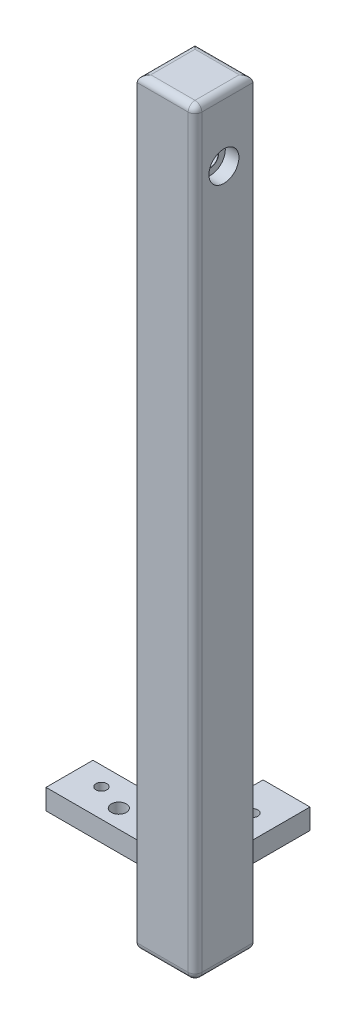
SolidWorks part; units mm, degrees
material "6061-T6 (SS)"
ref_plane "Front Plane" through (0, 0, 0) normal (0, 0, 1) x (1, 0, 0)
ref_plane "Top Plane" through (0, 0, 0) normal (0, 1, 0) x (1, 0, 0)
ref_plane "Right Plane" through (0, 0, 0) normal (1, 0, 0) x (0, 0, -1)
sketch "Sketch1" plane through (0, 0, 0) normal (0, 0, 1) x (1, 0, 0)
  line L0 (0, 0) -> (0, -111.5)
  line L1 (0, -111.5) -> (8.5, -111.5)
  line L2 (8.5, 0) -> (8.5, -111.5)
  line L7 (8.5, 0) -> (0, 0)
  dimension "D1" = 8.5
  dimension "D6" = 111.5
extrude "Boss-Extrude5" add sketch "Sketch1" along normal blind 8.5 contours L7 L0 L1 L2
hole_wizard "M5x0.8 Tapped Hole2" positions "Sketch26" profile "Sketch25" tap size "M5x0.8" standard "ANSI Metric"
sketch "Sketch26" plane through (0, -111.5, 0) normal (0, -1, 0) x (-1, 0, 0)
  point P0 (-4.25, -4.25)
sketch "Sketch25" plane through (4.25, -111.5, 4.25) normal (1, 0, 0) x (0, 0, -1)
  line L0 (0, 0) -> (0, 21.2618)
  line L1 (0, 21.2618) -> (2.1, 20)
  line L2 (2.1, 20) -> (2.1, 0)
  line L5 (2.1, 0) -> (0, 0)
  line L10 (0, 21.2618) -> (-2.1, 20) construction
  line L11 (0, -6.35) -> (0, 107.95) construction
  dimension "Tap Drill Dia." = 4.2
  dimension "Tap Drill Depth" = 20
  dimension "Drill Angle" = 118
cosmetic thread "Hole Thread4" parameters "D1"=10, "D2"=5
sketch "Sketch35" plane through (0, 0, 0) normal (-1, 0, 0) x (0, 0, 1)
  line L0 (0, 0) -> (0, -111.5) construction
  line L1 (0, -99) -> (8.5, -99)
  line L2 (0, -99) -> (0, -102)
  line L3 (0, -102) -> (8.5, -102)
  line L4 (8.5, -99) -> (8.5, -102)
  line L5 (8.5, 0) -> (8.5, -111.5) construction
  line L6 (8.5, -111.5) -> (0, -111.5) construction
  dimension "D1" = 9.5
  dimension "D2" = 3
extrude "Boss-Extrude6" add sketch "Sketch35" along normal blind 15
hole_wizard "Ø2.2 (2.2) Diameter Hole1" positions "Sketch37" profile "Sketch36" hole size "Ø2.2" standard "ANSI Metric"
sketch "Sketch37" plane through (0, -99, 0) normal (0, 1, 0) x (1, 0, 0)
  line L0 (-15, -8.5) -> (0, -8.5) construction
  line L2 (8.5, -8.5) -> (8.5, 0) construction
  point P0 (-7, -4.2)
  dimension "D1" = 4.3
  dimension "D2" = 15.5
sketch "Sketch36" plane through (-7, -99, 4.2) normal (1, 0, 0) x (0, 0, 1)
  line L0 (0, 0) -> (0, 13)
  line L1 (0, 13) -> (1.1, 13)
  line L2 (1.1, 13) -> (1.1, 0)
  line L5 (1.1, 0) -> (0, 0)
  line L10 (0, 13) -> (-1.1, 13) construction
  line L11 (0, -6.35) -> (0, 107.95) construction
  dimension "Hole Dia." = 2.2
  dimension "Hole Depth" = 13
  dimension "Drill Angle" = 180
hole_wizard "M2x0.4 Tapped Hole5" positions "Sketch39" profile "Sketch38" tap size "M2x0.4" standard "JIS" end condition up to next
sketch "Sketch39" plane through (0, -99, 0) normal (0, 1, 0) x (1, 0, 0)
  line L0 (8.5, -8.5) -> (8.5, 0) construction
  line L1 (-15, -8.5) -> (0, -8.5) construction
  point P0 (-11, -2.75)
  dimension "D1" = 19.5
  dimension "D2" = 5.75
cosmetic thread "Hole Thread6" parameters "D2"=2
sketch "Sketch38" plane through (-11, -99, 2.75) normal (1, 0, 0) x (0, 0, 1)
  line L0 (0, 0) -> (0, 3)
  line L1 (0, 3) -> (0.8, 3)
  line L2 (0.8, 3) -> (0.8, 0)
  line L5 (0.8, 0) -> (0, 0)
  line L11 (0, -6.35) -> (0, 107.95) construction
  dimension "Thru Tap Drill Dia." = 1.6
  dimension "Thru Tap Drill Depth" = 3
sketch "Sketch40" plane through (0, 0, 0) normal (0, 0, -1) x (-1, 0, 0)
  line L0 (-8.5, 0) -> (-8.5, -111.5) construction
  line L1 (0, -99) -> (-8.5, -99)
  line L2 (0, -99) -> (0, -102)
  line L3 (0, -102) -> (-8.5, -102)
  line L4 (-8.5, -99) -> (-8.5, -102)
  line L5 (0, -111.5) -> (-8.5, -111.5) construction
  dimension "D1" = 9.5
  dimension "D2" = 3
extrude "Boss-Extrude7" add sketch "Sketch40" along normal blind 10
hole_wizard "M2x0.4 Tapped Hole4" positions "Sketch42" profile "Sketch41" tap size "M2x0.4" standard "ANSI Metric" end condition up to next
sketch "Sketch42" plane through (0, -99, 0) normal (0, 1, 0) x (1, 0, 0)
  line L0 (0, 10) -> (8.5, 10) construction
  line L1 (0, 10) -> (0, 0) construction
  point P0 (3.45, 5)
  point P5 (0, 5)
  dimension "D1" = 5
  dimension "D2" = 3.45
sketch "Sketch41" plane through (3.45, -99, -5) normal (1, 0, 0) x (0, 0, 1)
  line L0 (0, 0) -> (0, 3)
  line L1 (0, 3) -> (0.8, 3)
  line L2 (0.8, 3) -> (0.8, 0)
  line L5 (0.8, 0) -> (0, 0)
  line L11 (0, -6.35) -> (0, 107.95) construction
  dimension "Thru Tap Drill Dia." = 1.6
  dimension "Thru Tap Drill Depth" = 3
cosmetic thread "Hole Thread11" parameters "D2"=2
hole_wizard "CBORE for M2 Socket Head Cap Screw1" positions "Sketch46" profile "Sketch45" counterbore size "M2" standard "JIS" end condition through all
sketch "Sketch46" plane through (8.5, 0, 0) normal (1, 0, 0) x (0, 0, -1)
  line L0 (-8.5, 0) -> (0, 0) construction
  point P0 (-4.25, -9.5)
  dimension "D1" = 9.5
sketch "Sketch45" plane through (8.5, -9.5, 4.25) normal (0, 1, 0) x (0, 0, -1)
  line L0 (0, 0) -> (0, 23.5)
  line L1 (0, 23.5) -> (1.2, 23.5)
  line L2 (1.2, 2.025) -> (1.2, 23.5)
  line L3 (1.2, 2.025) -> (1.225, 2)
  line L4 (1.225, 2) -> (2.2, 2)
  line L5 (2.2, 2) -> (2.2, 0)
  line L7 (0, 0) -> (2.2, 0)
  line L9 (-1.2, 2.025) -> (-1.225, 2) construction
  line L11 (0, -6.35) -> (0, 107.95) construction
  dimension "Thru Hole Dia." = 2.4
  dimension "Thru Hole Depth" = 23.5
  dimension "C'Bore Dia." = 4.4
  dimension "C'Bore Depth" = 2
  dimension "Mid C'Sink Dia." = 2.45
  dimension "Mid C'Sink Angle" = 90
fillet "Fillet1" radius 1 13 edges at (4.25, 0, 8.5) (4.25, -111.5, 2.15) (8.5, -55.75, 8.5) (4.25, 0, 0) (4.25, -111.5, 0) (4.25, -111.5, 8.5) (8.5, 0, 4.25) (0, 0, 4.25) (0, -111.5, 4.25) (8.5, -111.5, 4.25)
hole_wizard "M2x0.4 Tapped Hole3" positions "Sketch48" profile "Sketch47" tap size "M2x0.4" standard "ANSI Metric"
sketch "Sketch48" plane through (0, 0, 0) normal (0, 0, -1) x (-1, 0, 0)
  line L0 (-8.5, -1) -> (-8.5, -99) construction
  line L1 (-7.5, 0) -> (-1, 0) construction
  line L2 (-1, -111.5) -> (-7.5, -111.5) construction
  point P20 (-3.45, -26.8)
  point P25 (-3.45, -84.2)
  point P33 (-3.45, -31.1)
  point P35 (-3.45, -79.9)
  dimension "D1" = 5.05
  dimension "D2" = 5.05
  dimension "D3" = 26.8
  dimension "D4" = 27.3
  dimension "D5" = 4.3
  dimension "D6" = 4.3
  dimension "D7" = 5.05
  dimension "D8" = 5.05
sketch "Sketch47" plane through (3.45, -26.8, 0) normal (1, 0, 0) x (0, 1, 0)
  line L0 (0, 0) -> (0, 5.8009)
  line L1 (0, 5.8009) -> (1, 5.2)
  line L2 (1, 5.2) -> (1, 0)
  line L5 (1, 0) -> (0, 0)
  line L10 (0, 5.8009) -> (-1, 5.2) construction
  line L11 (0, -6.35) -> (0, 107.95) construction
  dimension "Tap Drill Dia." = 2
  dimension "Tap Drill Depth" = 5.2
  dimension "Drill Angle" = 118
cosmetic thread "Hole Thread7" parameters "D1"=4, "D2"=2
cosmetic thread "Hole Thread8" parameters "D1"=4, "D2"=2
cosmetic thread "Hole Thread9" parameters "D1"=4, "D2"=2
cosmetic thread "Hole Thread10" parameters "D1"=4, "D2"=2
sketch "Sketch49" plane through (0, -99, 0) normal (0, 1, 0) x (1, 0, 0)
  line L0 (0, 10) -> (8.5, 10) construction
  line L1 (8.5, 0) -> (6.9, 0)
  line L2 (8.5, 0) -> (8.5, 10)
  line L3 (8.5, 10) -> (6.9, 10)
  line L4 (6.9, 0) -> (6.9, 10)
  line L5 (0, -8.5) -> (0, 0) construction
  line L6 (-15, -8.5) -> (0, -8.5)
  line L7 (-15, -8.5) -> (-15, -6.9)
  line L8 (-15, -6.9) -> (0, -6.9)
  line L9 (0, -8.5) -> (0, -6.9)
  dimension "D1" = 1.6
  dimension "D2" = 1.6
extrude "Cut-Extrude1" cut sketch "Sketch49" against normal blind 10
